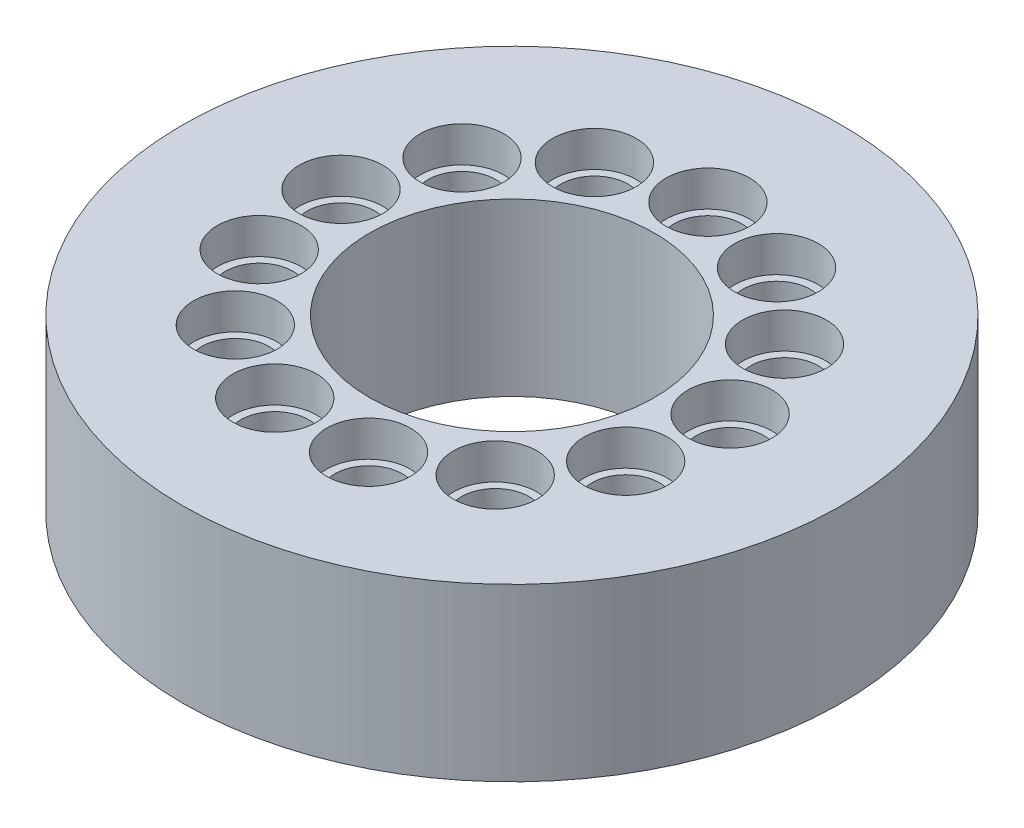
SolidWorks part; units mm, degrees
ref_plane "Front Plane" through (0, 0, 0) normal (0, 0, 1) x (1, 0, 0)
ref_plane "Top Plane" through (0, 0, 0) normal (0, 1, 0) x (1, 0, 0)
ref_plane "Right Plane" through (0, 0, 0) normal (1, 0, 0) x (0, 0, -1)
sketch "Sketch2" plane through (0, 0, 0) normal (0, 1, 0) x (1, 0, 0)
  circle A0 centre (0, 0) radius 9.25
  circle A1 centre (0, 0) radius 5.5 construction
  circle A2 centre (0, 0) radius 4
  dimension "D1" = 18.5
  dimension "D2" = 5.5
  dimension "D3" = 8
extrude "Boss-Extrude1" add sketch "Sketch2" along normal blind 4.8
hole_wizard "Hole1" positions "Sketch3" profile "Sketch4" legacy end condition up to next
sketch "Sketch3" plane through (0, 4.8, 0) normal (0, 1, 0) x (1, 0, 0)
  circle A0 centre (0, 0) radius 5.5 construction
  point P0 (0, 5.5)
sketch "Sketch4" plane through (0, 4.8, -5.5) normal (1, 0, 0) x (0, 0, 1)
  line L0 (0, 0) -> (0, 4.801)
  line L1 (0, 4.801) -> (0.95, 4.801)
  line L2 (0.95, 4.801) -> (0.95, 1)
  line L3 (0.95, 1) -> (1.175, 1)
  line L4 (1.175, 1) -> (1.175, 0)
  line L5 (1.175, 0) -> (0, 0)
  line L6 (0, 110) -> (0, -10) construction
  dimension "Diameter" = 1.9
  dimension "Depth" = 4.801
  dimension "C-Bore Diameter" = 2.35
  dimension "C-Bore Depth" = 1
pattern_circular "CirPattern1" count 13 over 360 about axis through (0, 0, 0) along (0, 1, 0) of "Hole1"
